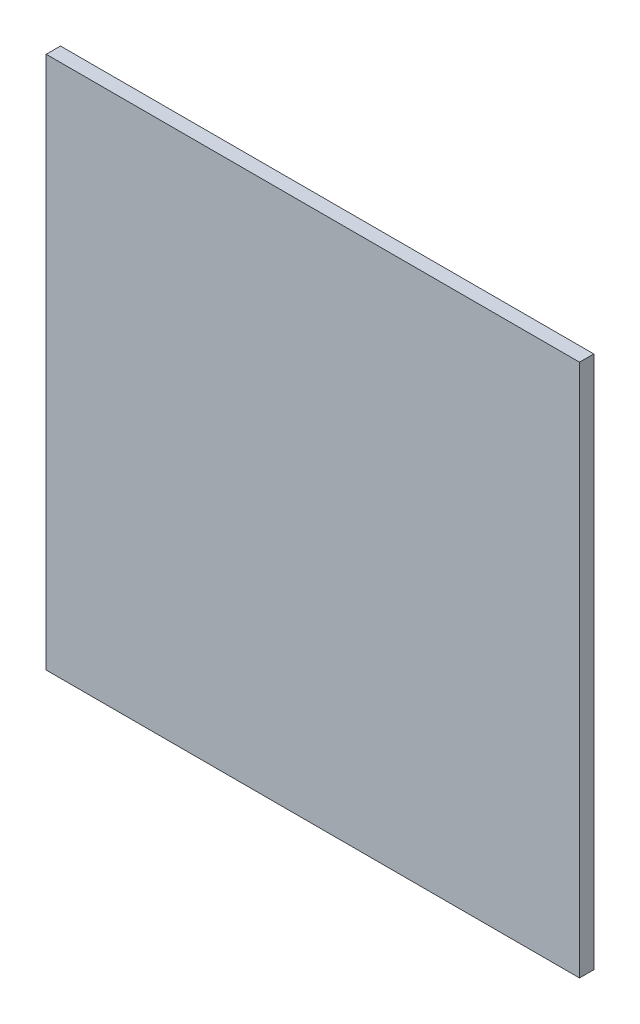
SolidWorks part; units mm, degrees
material "A-Glass Fiber"
ref_plane "Front Plane" through (0, 0, 0) normal (0, 0, 1) x (1, 0, 0)
ref_plane "Top Plane" through (0, 0, 0) normal (0, 1, 0) x (1, 0, 0)
ref_plane "Right Plane" through (0, 0, 0) normal (1, 0, 0) x (0, 0, -1)
sketch "Sketch1" plane through (0, 0, 0) normal (0, 0, 1) x (1, 0, 0)
  line L1 (-28, 28) -> (28, 28)
  line L2 (-28, 28) -> (-28, -28)
  line L3 (-28, -28) -> (28, -28)
  line L4 (28, 28) -> (28, -28)
  line L5 (-28, 28) -> (28, -28) construction
  line L6 (-28, -28) -> (28, 28) construction
  point P0 (0, 0)
  dimension "D1" = 56
  dimension "D2" = 56
extrude "Boss-Extrude1" add sketch "Sketch1" along normal blind 1.5 contours L2 L3 L4 L1
